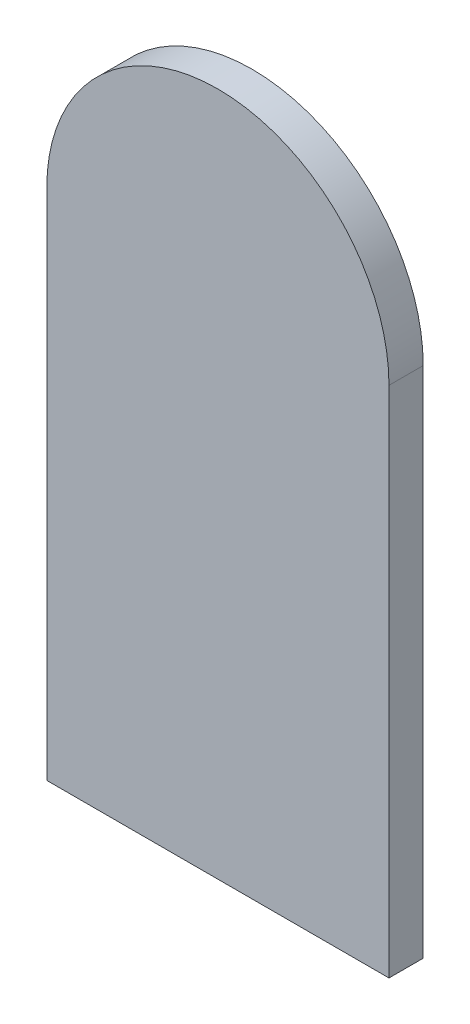
SolidWorks part; units mm, degrees
ref_plane "Plan de face" through (0, 0, 0) normal (0, 0, 1) x (1, 0, 0)
ref_plane "Plan de dessus" through (0, 0, 0) normal (0, 1, 0) x (1, 0, 0)
ref_plane "Plan de droite" through (0, 0, 0) normal (1, 0, 0) x (0, 0, -1)
sketch "Esquisse1" plane through (0, 0, 0) normal (0, 0, 1) x (1, 0, 0)
  line L0 (-10, 0) -> (-10, 30)
  line L1 (10, 30) -> (10, 0)
  line L2 (10, 0) -> (-10, 0)
  arc A0 (-10, 30) -> (10, 30) centre (0, 30) cw
  point P4 (0, 0)
  dimension "D2" = 30
  dimension "D1" = 20
extrude "Boss.-Extru.1" add sketch "Esquisse1" along normal blind 2 contours L0 A0 L1 L2
